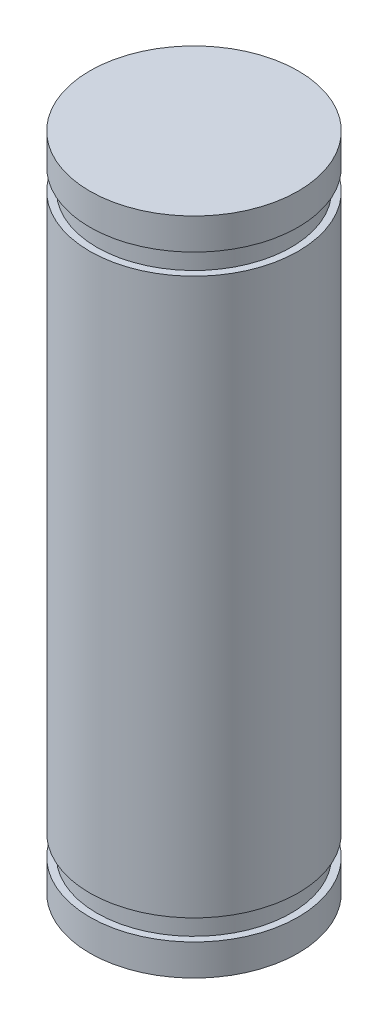
SolidWorks part; units mm, degrees
ref_plane "前视基准面" through (0, 0, 0) normal (0, 0, 1) x (1, 0, 0)
ref_plane "上视基准面" through (0, 0, 0) normal (0, 1, 0) x (1, 0, 0)
ref_plane "右视基准面" through (0, 0, 0) normal (1, 0, 0) x (0, 0, -1)
sketch "草图1" plane through (0, 0, 0) normal (0, 0, 1) x (1, 0, 0)
  line L0 (0, -9.5) -> (3, -9.5)
  line L1 (3, -9.5) -> (3, -8.6)
  line L2 (3, -8.6) -> (2.8, -8.6)
  line L3 (2.8, -8.6) -> (2.8, -8)
  line L4 (2.8, -8) -> (3, -8)
  line L5 (3, -8) -> (3, 8)
  line L6 (3, 8) -> (2.8, 8)
  line L7 (2.8, 8.6) -> (3, 8.6)
  line L8 (2.8, 8) -> (2.8, 8.6)
  line L9 (3, 8.6) -> (3, 9.5)
  line L10 (3, 9.5) -> (0, 9.5)
  line L11 (0, 9.5) -> (0, -9.5)
  dimension "D1" = 3
  dimension "D2" = 0.2
  dimension "D3" = 19
  dimension "D4" = 0.6
  dimension "D5" = 0.9
revolve "旋转1" add sketch "草图1" angle 360 about L11
